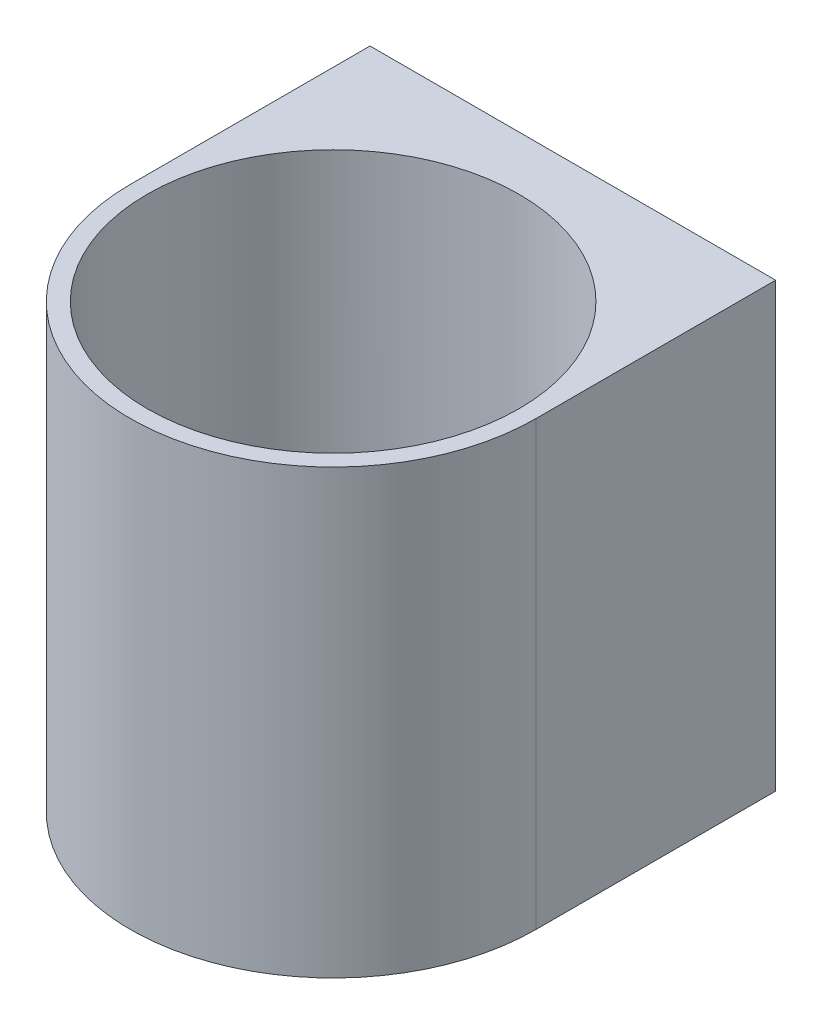
SolidWorks part; units mm, degrees
ref_plane "Front Plane" through (0, 0, 0) normal (0, 0, 1) x (1, 0, 0)
ref_plane "Top Plane" through (0, 0, 0) normal (0, 1, 0) x (1, 0, 0)
ref_plane "Right Plane" through (0, 0, 0) normal (1, 0, 0) x (0, 0, -1)
sketch "Sketch1" plane through (0, 0, 0) normal (0, 1, 0) x (1, 0, 0)
  line L1 (-45.5066, 16.4638) -> (9.4934, 16.4638)
  line L2 (-45.5066, 16.4638) -> (-45.5066, -16.0362)
  line L3 (-45.5066, -16.0362) -> (9.4934, -16.0362)
  line L4 (9.4934, 16.4638) -> (9.4934, -16.0362)
  circle A0 centre (-18.0066, -16.0362) radius 27.5
  circle A1 centre (-18.0066, -16.0362) radius 25.2
  dimension "D1" = 32.5
  dimension "D2" = 55
extrude "Boss-Extrude2" add sketch "Sketch1" along normal blind 60 contours A0 L4 L1 L2 | L3 A1 | L3 A1
sketch "Sketch3" plane through (0, 0, 0) normal (0, -1, 0) x (-1, 0, 0)
  circle A0 centre (18.0066, -16.0362) radius 25.2
extrude "Boss-Extrude3" add sketch "Sketch3" against normal blind 9.3
sketch "Sketch4" plane through (0, 9.3, 0) normal (0, 1, 0) x (1, 0, 0)
  line L0 (-18.0066, -41.2362) -> (-18.0066, 9.1638)
  line L1 (-43.2066, -16.0362) -> (7.1934, -16.0362)
  circle A0 centre (-18.0066, -16.0362) radius 25.2 construction
  circle A1 centre (-18.0066, -16.0362) radius 25.2 construction
  circle A2 centre (-18.0066, -16.0362) radius 3.5
  circle A3 centre (-8.0066, -16.0362) radius 3.5
  circle A4 centre (1.9934, -16.0362) radius 3.5
  circle A5 centre (-18.0066, -6.0362) radius 3.5
  circle A6 centre (-18.0066, 3.9638) radius 3.5
  circle A7 centre (-28.0066, -16.0362) radius 3.5
  circle A8 centre (-38.0066, -16.0362) radius 3.5
  circle A9 centre (-18.0066, -26.0362) radius 3.5
  circle A10 centre (-18.0066, -36.0362) radius 3.5
  circle A11 centre (-28.0066, -6.0362) radius 3.5
  circle A12 centre (-8.0066, -6.0362) radius 3.5
  circle A13 centre (-8.0066, -26.0362) radius 3.5
  circle A14 centre (-28.0066, -26.0362) radius 3.5
  dimension "D1" = 10
  dimension "D2" = 10
  dimension "D3" = 10
  dimension "D4" = 10
  dimension "D5" = 10
  dimension "D6" = 10
  dimension "D7" = 10
  dimension "D8" = 10
extrude "Cut-Extrude1" cut sketch "Sketch4" against normal blind 9.3 contours L0 A6 | L0 A6 | L0 A5 | L0 A5 | A11 | A12 | L1 A3 | L1 A3 | L1 A4 | L1 A4 | L0 A2 L1 | L0 A2 L1 | L1 A2 L0 | L1 A2 L0 | L1 A8 | L1 A8 | A14 | L0 A9 | L0 A9 | A13 | L0 A10 | L0 A10 | L1 A7 | L1 A7
